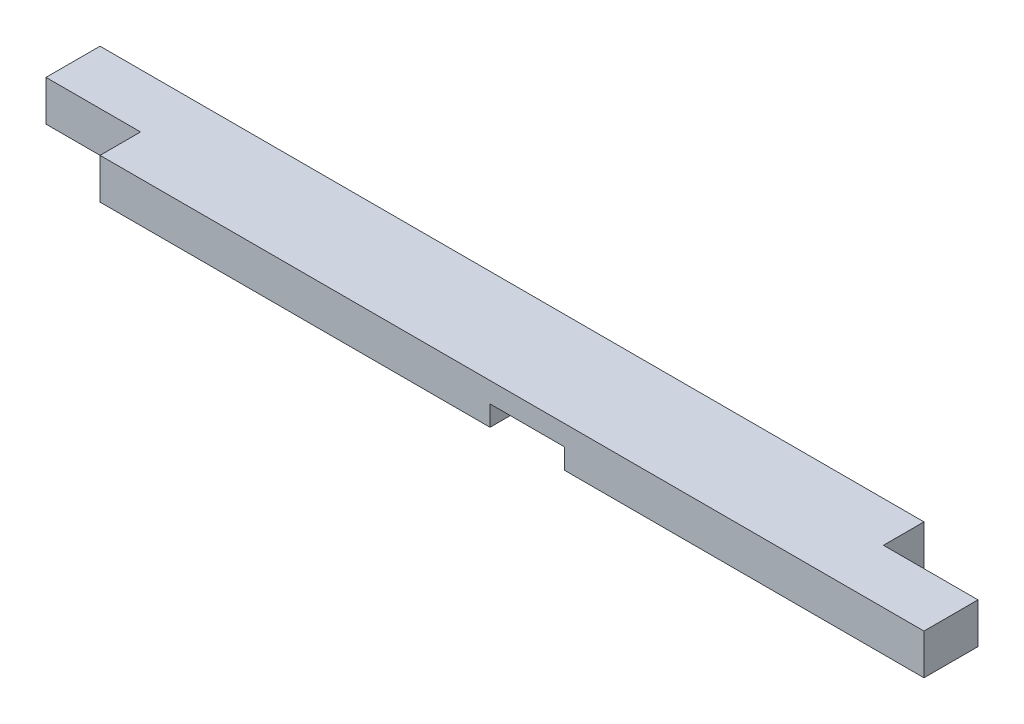
SolidWorks part; units mm, degrees
material "Pine"
ref_plane "Front Plane" through (0, 0, 0) normal (0, 0, 1) x (1, 0, 0)
ref_plane "Top Plane" through (0, 0, 0) normal (0, 1, 0) x (1, 0, 0)
ref_plane "Right Plane" through (0, 0, 0) normal (1, 0, 0) x (0, 0, -1)
sketch "Sketch1" plane through (0, 0, 0) normal (0, 1, 0) x (1, 0, 0)
  line L1 (0, 0) -> (863.6, 0)
  line L2 (0, 0) -> (0, 88.9)
  line L3 (0, 88.9) -> (863.6, 88.9)
  line L4 (863.6, 0) -> (863.6, 88.9)
  dimension "D1" = 88.9
  dimension "D2" = 863.6
extrude "Boss-Extrude1" add sketch "Sketch1" along normal blind 38.1
sketch "Sketch3" plane through (0, 38.1, 0) normal (0, 1, 0) x (1, 0, 0)
  line L1 (863.6, 88.9) -> (774.7, 88.9)
  line L2 (863.6, 88.9) -> (863.6, 50.8)
  line L3 (863.6, 50.8) -> (774.7, 50.8)
  line L4 (774.7, 88.9) -> (774.7, 50.8)
  dimension "D1" = 774.7
  dimension "D2" = 38.1
extrude "Cut-Extrude2" cut sketch "Sketch3" against normal through all
sketch "Sketch4" plane through (0, 0, -88.9) normal (0, 0, -1) x (-1, 0, 0)
  line L1 (-525.4625, 19.05) -> (-455.6125, 19.05)
  line L2 (-525.4625, 19.05) -> (-525.4625, 0)
  line L3 (-525.4625, 0) -> (-455.6125, 0)
  line L5 (-774.7, 0) -> (0, 0) construction
  line L6 (-455.6125, 19.05) -> (-455.6125, 0)
  dimension "D1" = 19.05
  dimension "D2" = 455.6125
  dimension "D3" = 69.85
extrude "Cut-Extrude3" cut sketch "Sketch4" against normal through all
sketch "Sketch5" plane through (0, 0, 0) normal (0, -1, 0) x (1, 0, 0)
  line L1 (0, 0) -> (88.9, 0)
  line L2 (0, 0) -> (0, -38.1)
  line L3 (0, -38.1) -> (88.9, -38.1)
  line L4 (88.9, 0) -> (88.9, -38.1)
  dimension "D1" = 38.1
  dimension "D2" = 88.9
extrude "Cut-Extrude4" cut sketch "Sketch5" against normal through all
